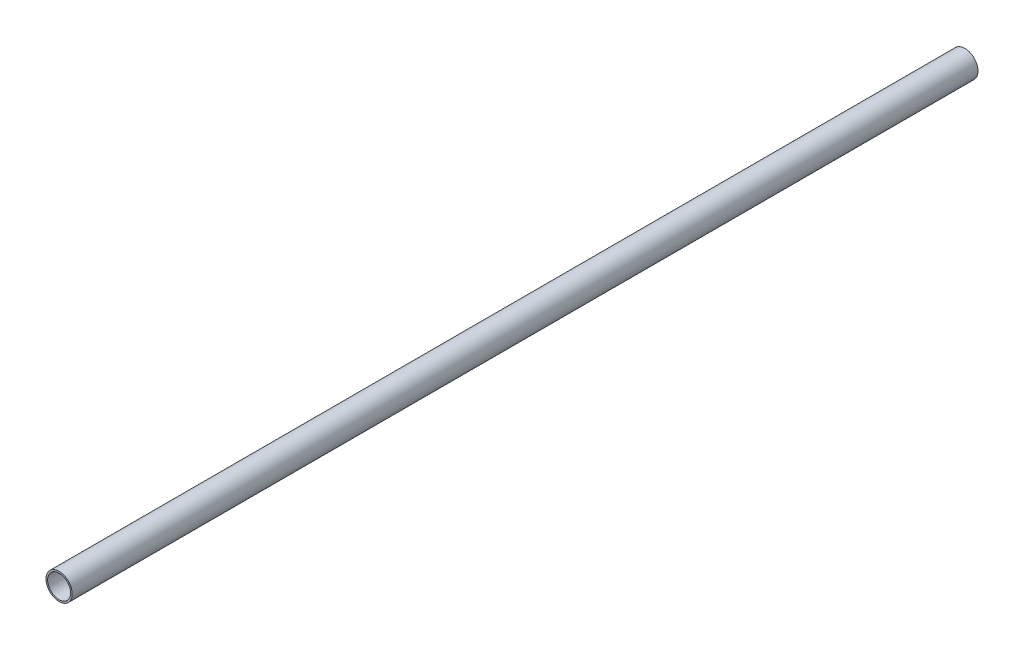
SolidWorks part; units mm, degrees
material "Литая легированная сталь"
ref_plane "Спереди" through (0, 0, 0) normal (0, 0, 1) x (1, 0, 0)
ref_plane "Сверху" through (0, 0, 0) normal (0, 1, 0) x (1, 0, 0)
ref_plane "Справа" through (0, 0, 0) normal (1, 0, 0) x (0, 0, -1)
sketch "Эскиз1" plane through (0, 0, 0) normal (0, 0, 1) x (1, 0, 0)
  circle A0 centre (0, 0) radius 8
  circle A1 centre (0, 0) radius 7
  dimension "D1" = 16
  dimension "D2" = 14
extrude "Бобышка-Вытянуть1" add sketch "Эскиз1" along normal blind 552
